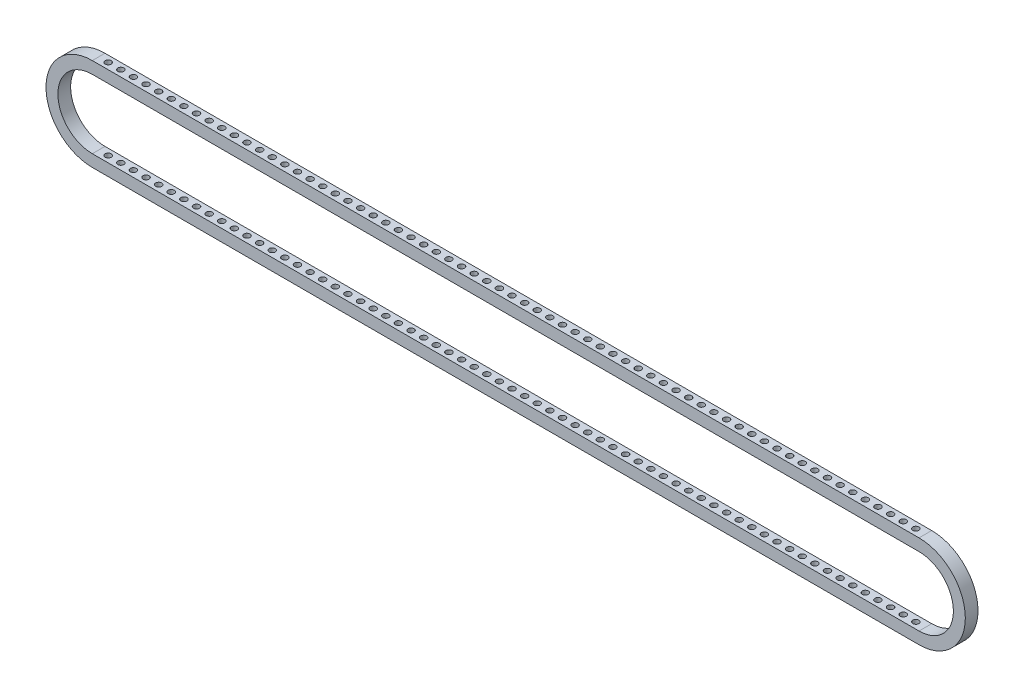
SolidWorks part; units mm, degrees
material "AISI 1020"
ref_plane "前视基准面" through (0, 0, 0) normal (0, 0, 1) x (1, 0, 0)
ref_plane "上视基准面" through (0, 0, 0) normal (0, 1, 0) x (1, 0, 0)
ref_plane "右视基准面" through (0, 0, 0) normal (1, 0, 0) x (0, 0, -1)
sketch "草图1" plane through (0, 0, 0) normal (0, 0, 1) x (1, 0, 0)
  line L0 (-208, 0) -> (208, 0) construction
  line L1 (-208, 23.295) -> (208, 23.295)
  line L2 (-208, -23.295) -> (208, -23.295)
  line L3 (-208, 17.295) -> (208, 17.295)
  line L4 (-208, -17.295) -> (208, -17.295)
  circle A0 centre (-208, 0) radius 20.295 construction
  circle A1 centre (208, 0) radius 20.295 construction
  arc A2 (-208, 23.295) -> (-208, -23.295) centre (-208, 0) ccw
  arc A3 (208, -23.295) -> (208, 23.295) centre (208, 0) ccw
  arc A4 (-208, 17.295) -> (-208, -17.295) centre (-208, 0) ccw
  arc A5 (208, -17.295) -> (208, 17.295) centre (208, 0) ccw
  circle A6 centre (-208, 0) radius 23.295 construction
  circle A7 centre (208, 0) radius 23.295 construction
  circle A8 centre (-208, 0) radius 17.295 construction
  circle A9 centre (208, 0) radius 17.295 construction
  point P4 (0, 0)
  dimension "D2" = 40.59
  dimension "D1" = 416
  dimension "D3" = 3
  dimension "D4" = 3
  dimension "D5" = 3
  dimension "D6" = 3
extrude "凸台-拉伸1" add sketch "草图1" along normal mid plane 6.38
sketch "草图2" plane through (0, -23.295, 0) normal (0, -1, 0) x (1, 0, 0)
  circle A0 centre (0, 0) radius 1.525
  dimension "D1" = 3.05
extrude "切除-拉伸1" cut sketch "草图2" against normal through all both and the other way through all
pattern_linear "阵列(线性)1" count 33 spacing 6.35 along (1, 0, 0) count 33 spacing 6.35 along (-1, 0, 0) of "切除-拉伸1"
